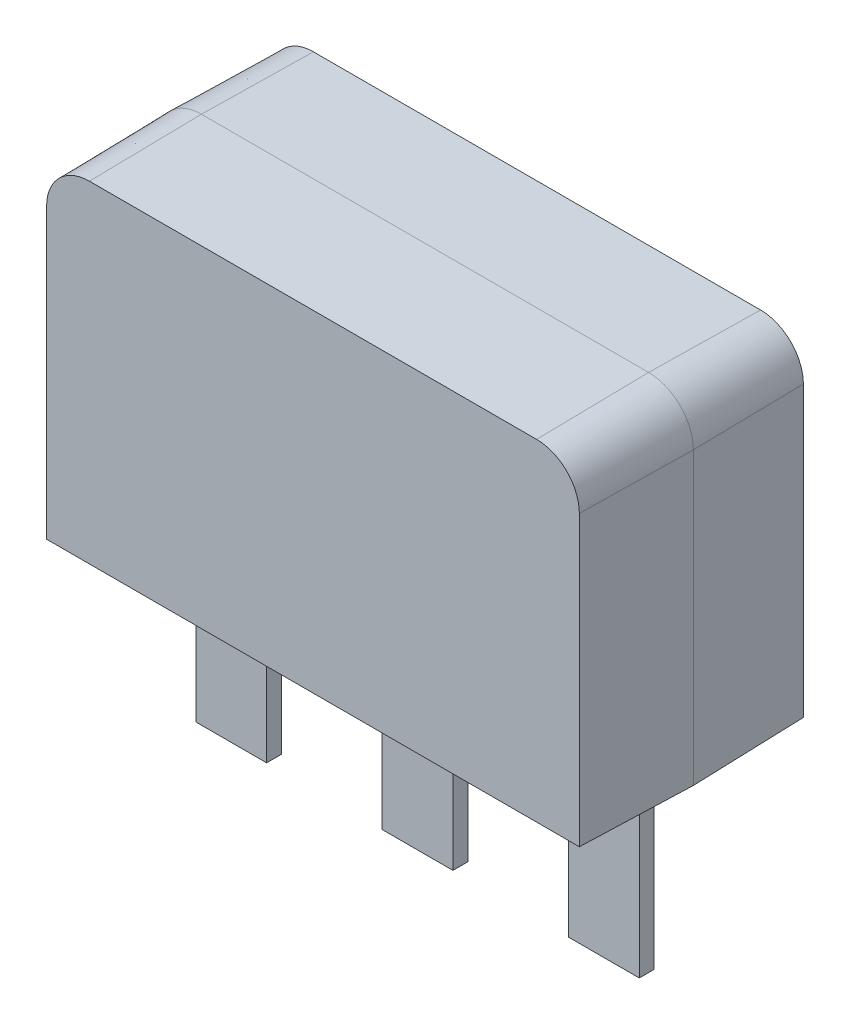
SolidWorks part; units mm, degrees
ref_plane "Front Plane" through (0, 0, 0) normal (0, 0, 1) x (1, 0, 0)
ref_plane "Top Plane" through (0, 0, 0) normal (0, 1, 0) x (1, 0, 0)
ref_plane "Right Plane" through (0, 0, 0) normal (1, 0, 0) x (0, 0, -1)
sketch "Sketch1" plane through (0, 0, 0) normal (0, 0, 1) x (1, 0, 0)
  line L0 (3600, 0) -> (-3600, 0)
  line L2 (-3000, 4500) -> (3000, 4500)
  line L3 (-3600, 0) -> (-3600, 3900)
  line L4 (3600, 0) -> (3600, 3900)
  arc A0 (-3600, 3900) -> (-3000, 4500) centre (-3000, 3900) cw
  arc A1 (3000, 4500) -> (3600, 3900) centre (3000, 3900) cw
  dimension "D1" = 600
  dimension "D2" = 600
sketch "Sketch2" plane through (0, 0, 0) normal (1, 0, 0) x (0, 0, -1)
  line L0 (-1500, 0) -> (1500, 0)
  line L1 (-1500, 0) -> (-1500, 4500)
  line L2 (-1500, 4500) -> (1500, 4500)
  line L3 (1500, 4500) -> (1500, 0)
  line L4 (-100, 0) -> (-100, -2500)
  line L5 (-100, -2500) -> (100, -2500)
  line L6 (100, -2500) -> (100, 0)
sketch "Sketch3" plane through (0, 0, 0) normal (0, 1, 0) x (1, 0, 0)
  line L1 (-2975, 100) -> (-2025, 100)
  line L2 (-2025, 100) -> (-2025, -100)
  line L5 (-2025, -100) -> (-2975, -100)
  line L9 (-2975, -100) -> (-2975, 100)
  line L12 (2975, -100) -> (2975, 100)
  line L13 (2025, -100) -> (2975, -100)
  line L14 (2025, 100) -> (2025, -100)
  line L15 (2975, 100) -> (2025, 100)
  line L17 (475, -100) -> (475, 100)
  line L18 (-475, -100) -> (475, -100)
  line L19 (-475, 100) -> (-475, -100)
  line L20 (475, 100) -> (-475, 100)
sketch "Sketch4" plane through (0, 0, 0) normal (0, 1, 0) x (1, 0, 0)
  point P8 (0, 0)
extrude "Boss-Extrude1" add sketch "Sketch3" against normal blind 2499
extrude "Boss-Extrude3" add sketch "Sketch1" along normal mid plane 3006 draft 1 separate body
